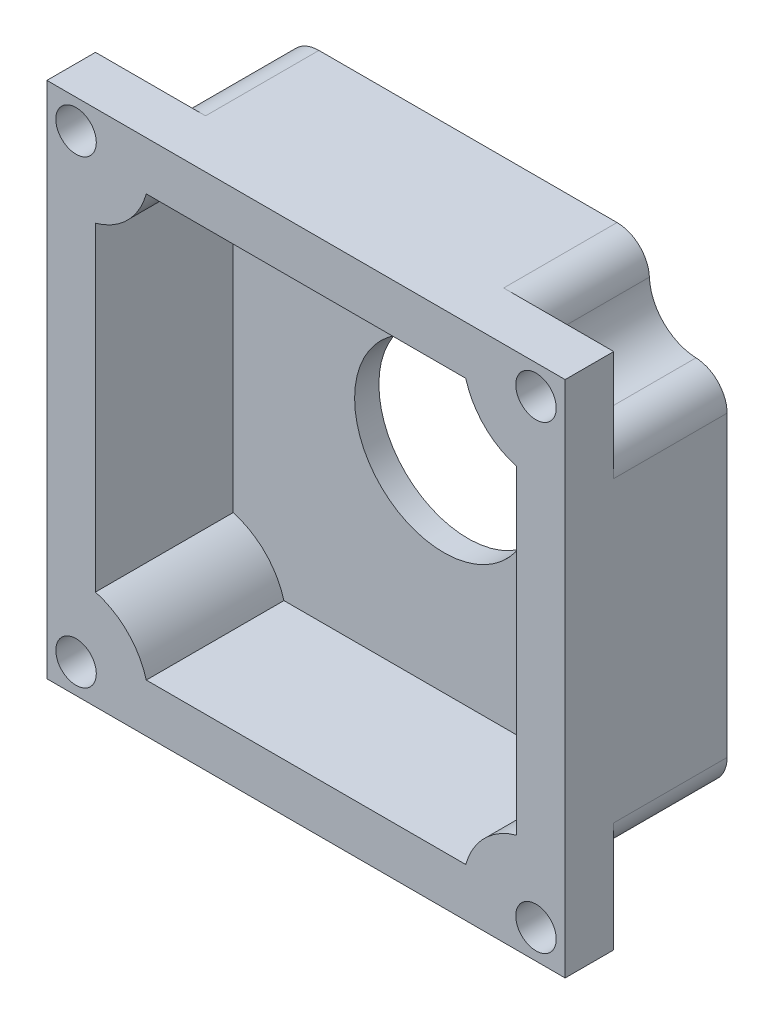
SolidWorks part; units mm, degrees
ref_plane "前视基准面" through (0, 0, 0) normal (0, 0, 1) x (1, 0, 0)
ref_plane "上视基准面" through (0, 0, 0) normal (0, 1, 0) x (1, 0, 0)
ref_plane "右视基准面" through (0, 0, 0) normal (1, 0, 0) x (0, 0, -1)
other "Configuration Table"
sketch "Sketch1" plane through (0, 0, 0) normal (0, 0, 1) x (1, 0, 0)
  line L0 (-13, -13) -> (-13, 13)
  line L1 (16, -16) -> (-16, -16)
  line L2 (16, -16) -> (16, 16)
  line L3 (16, 16) -> (-16, 16)
  line L4 (-16, -16) -> (-16, 16)
  line L5 (16, -16) -> (-16, 16) construction
  line L6 (16, 16) -> (-16, -16) construction
  line L7 (13, 13) -> (-13, 13)
  line L8 (13, -13) -> (13, 13)
  line L9 (13, -13) -> (-13, -13)
  point P0 (0, 0)
  dimension "D1" = 32
  dimension "D2" = 32
  dimension "D3" = 3
extrude "Boss-Extrude1" add sketch "Sketch1" along normal blind 10
sketch "Sketch2" plane through (0, 0, 0) normal (0, 0, -1) x (-1, 0, 0)
  line L1 (-13, 13) -> (13, 13)
  line L2 (-13, 13) -> (-13, -13)
  line L3 (-13, -13) -> (13, -13)
  line L4 (13, 13) -> (13, -13)
extrude "Boss-Extrude2" add sketch "Sketch2" against normal blind 1.5
sketch "Sketch3" plane through (0, 0, 0) normal (0, 0, -1) x (-1, 0, 0)
  circle A0 centre (0, 0) radius 5.5
  dimension "D1" = 11
extrude "Cut-Extrude1" cut sketch "Sketch3" against normal blind 9.5
sketch "Sketch4" plane through (0, 0, 0) normal (0, 0, -1) x (-1, 0, 0)
  line L0 (-16, -16) -> (-16, 16) construction
  line L1 (-16, 16) -> (16, 16) construction
  line L2 (0, 5.5) -> (0, -5.5) construction
  line L3 (-5.5, 0) -> (5.5, 0) construction
  circle A0 centre (-14.2, 14.2) radius 1.25
  circle A1 centre (0, 0) radius 5.5 construction
  circle A2 centre (14.2, 14.2) radius 1.25
  circle A3 centre (14.2, -14.2) radius 1.25
  circle A4 centre (-14.2, -14.2) radius 1.25
  dimension "D3" = 2.5
  dimension "D1" = 1.8
  dimension "D2" = 1.8
extrude "Cut-Extrude2" cut sketch "Sketch4" against normal blind 21.5
sketch "Sketch6" plane through (0, 0, 0) normal (0, 0, -1) x (-1, 0, 0)
  line L0 (0, 5.5) -> (0, -5.5) construction
  line L1 (-5.5, 0) -> (5.5, 0) construction
  circle A0 centre (-14.2, 14.2) radius 3
  circle A1 centre (0, 0) radius 5.5 construction
  circle A2 centre (14.2, 14.2) radius 3
  circle A3 centre (14.2, -14.2) radius 3
  circle A4 centre (-14.2, -14.2) radius 3
  dimension "D1" = 6
extrude "Cut-Extrude3" cut sketch "Sketch6" against normal blind 7
sketch "Sketch7" plane through (0, 0, 7) normal (0, 0, -1) x (-1, 0, 0)
  line L0 (11.8, 16) -> (16, 16)
  line L1 (16, 16) -> (16, 11.8)
  circle A0 centre (14.2, 14.2) radius 3
  circle A1 centre (14.2, 14.2) radius 1.25
  line M3 (11.4505, 13) -> (13, 13)
  line M4 (13, 13) -> (13, 11.4505)
  arc M5 (13, 11.4505) -> (16, 11.8) centre (14.2, 14.2) ccw
  line M6 (16, 11.8) -> (16, 16)
  line M7 (16, 16) -> (11.8, 16)
  arc M8 (11.8, 16) -> (11.4505, 13) centre (14.2, 14.2) ccw
  circle M9 centre (14.2, 14.2) radius 1.25
extrude "Boss-Extrude3" add sketch "Sketch7" against normal blind 3 contours M8 M3 M4 M5 M6 M7 M9 | A0 M3 M4
pattern_circular "CirPattern1" count 4 every 90 about axis through (0, 0, 9.5) along (0, 0, -1) of "Boss-Extrude3"
sketch "Sketch8" plane through (0, 0, 1.5) normal (0, 0, 1) x (1, 0, 0)
  line L0 (-13, 11.4505) -> (-13, 9.863)
  line L1 (-13, -11.4505) -> (-13, 11.4505) construction
  line L2 (-11.4505, 13) -> (-9.863, 13)
  line L3 (11.4505, 13) -> (-11.4505, 13) construction
  circle A0 centre (-14.2, 14.2) radius 3
  circle A1 centre (-14.2, 14.2) radius 4.5
  line M7 (11.4505, 13) -> (-11.4505, 13)
  arc M8 (-11.4505, 13) -> (-13, 11.4505) centre (-14.2, 14.2) cw
  line M9 (-13, 11.4505) -> (-13, -11.4505)
  dimension "D1" = 6
  dimension "D2" = 9
extrude "Boss-Extrude4" add sketch "Sketch8" along normal blind 8.5 contours A1 M9 M7 M8
pattern_circular "CirPattern2" count 4 every 90 about axis through (0, 0, 0) along (0, 0, 1) of "Boss-Extrude4"
fillet "Fillet1" radius 2 8 edges at (-11.8, 16, 3.5) (-16, 11.8, 3.5) (-16, -11.8, 3.5) (-11.8, -16, 3.5) (11.8, -16, 3.5) (16, -11.8, 3.5) (16, 11.8, 3.5) (11.8, 16, 3.5)
